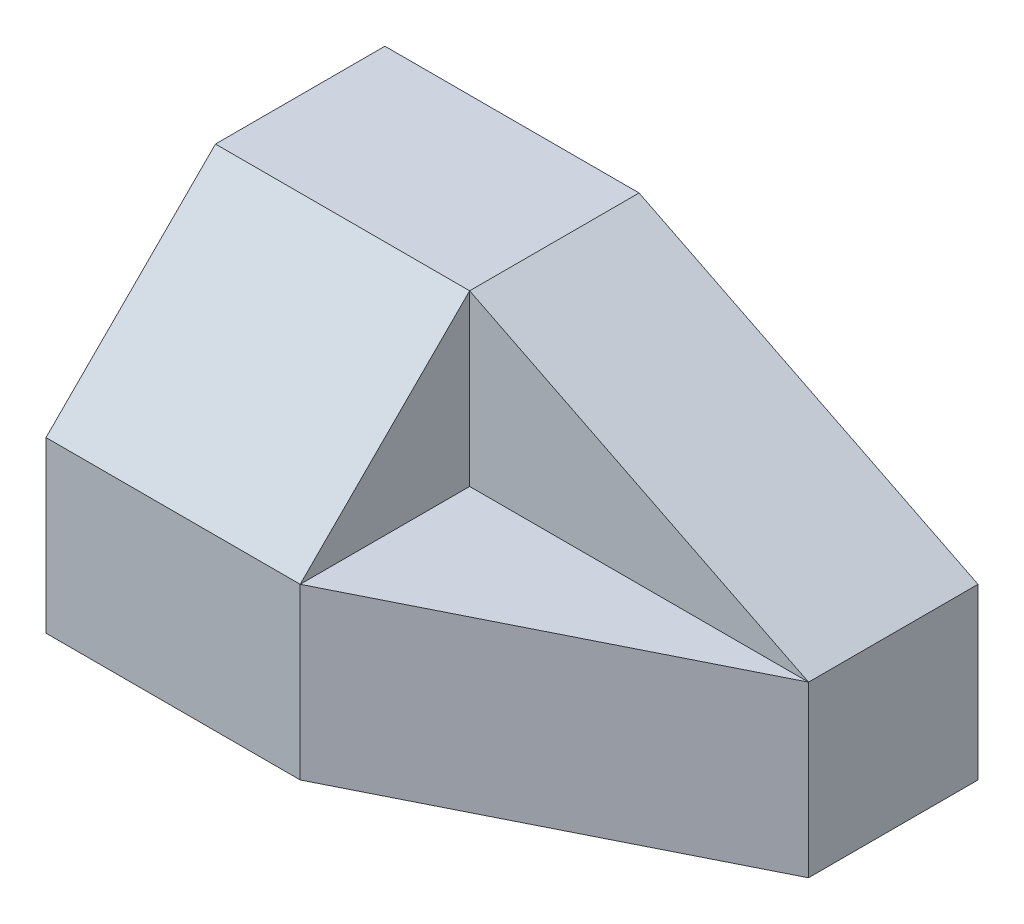
SolidWorks part; units mm, degrees
ref_plane "前基準面" through (0, 0, 0) normal (0, 0, 1) x (1, 0, 0)
ref_plane "上基準面" through (0, 0, 0) normal (0, 1, 0) x (1, 0, 0)
ref_plane "右基準面" through (0, 0, 0) normal (1, 0, 0) x (0, 0, -1)
sketch "草圖1" plane through (0, 0, 0) normal (0, 1, 0) x (1, 0, 0)
  line L1 (-17.5, -10) -> (17.5, -10)
  line L2 (-17.5, -10) -> (-17.5, 10)
  line L3 (-17.5, 10) -> (17.5, 10)
  line L4 (17.5, -10) -> (17.5, 10)
  line L5 (-17.5, -10) -> (17.5, 10) construction
  line L6 (-17.5, 10) -> (17.5, -10) construction
  point P0 (0, 0)
  dimension "D1" = 35
  dimension "D2" = 20
extrude "填料-伸長1" add sketch "草圖1" along normal blind 20
sketch "草圖2" plane through (0, 0, 10) normal (0, 0, 1) x (1, 0, 0)
  line L0 (17.5, 20) -> (-2.5, 20)
  line L1 (-17.5, 20) -> (17.5, 20) construction
  line L2 (-2.5, 20) -> (17.5, 10)
  line L3 (17.5, 20) -> (17.5, 0) construction
  line L4 (17.5, 10) -> (17.5, 20)
  dimension "D1" = 20
  dimension "D2" = 10
extrude "除料-伸長1" cut sketch "草圖2" against normal blind 20
sketch "草圖3" plane through (0, 0, 0) normal (0, 1, 0) x (1, 0, 0)
  line L0 (-2.5, -10) -> (17.5, -10)
  line L1 (-2.5, -10) -> (17.5, -10) construction
  line L2 (17.5, -10) -> (17.5, 0)
  line L3 (17.5, 10) -> (17.5, -10) construction
  line L4 (17.5, 0) -> (-2.5, -10)
  dimension "D1" = 20
  dimension "D2" = 10
extrude "除料-伸長2" cut sketch "草圖3" along normal blind 32 contours L4 L0 L2
sketch "草圖4" plane through (0, 20, 0) normal (0, 1, 0) x (1, 0, 0)
  line L0 (17.5, 0) -> (-2.5, 0)
  line L1 (-2.5, 10) -> (-2.5, -10) construction
  line L2 (-2.5, 0) -> (-2.5, -10)
  line L3 (-2.5, -10) -> (17.5, 0)
extrude "除料-伸長3" cut sketch "草圖4" against normal blind 10
sketch "草圖5" plane through (-2.5, 0, 0) normal (1, 0, 0) x (0, 0, -1)
  line L0 (0, 20) -> (-10, 20)
  line L1 (-10, 20) -> (-10, 10)
  line L2 (-10, 10) -> (0, 20)
extrude "除料-伸長4" cut sketch "草圖5" against normal blind 19
